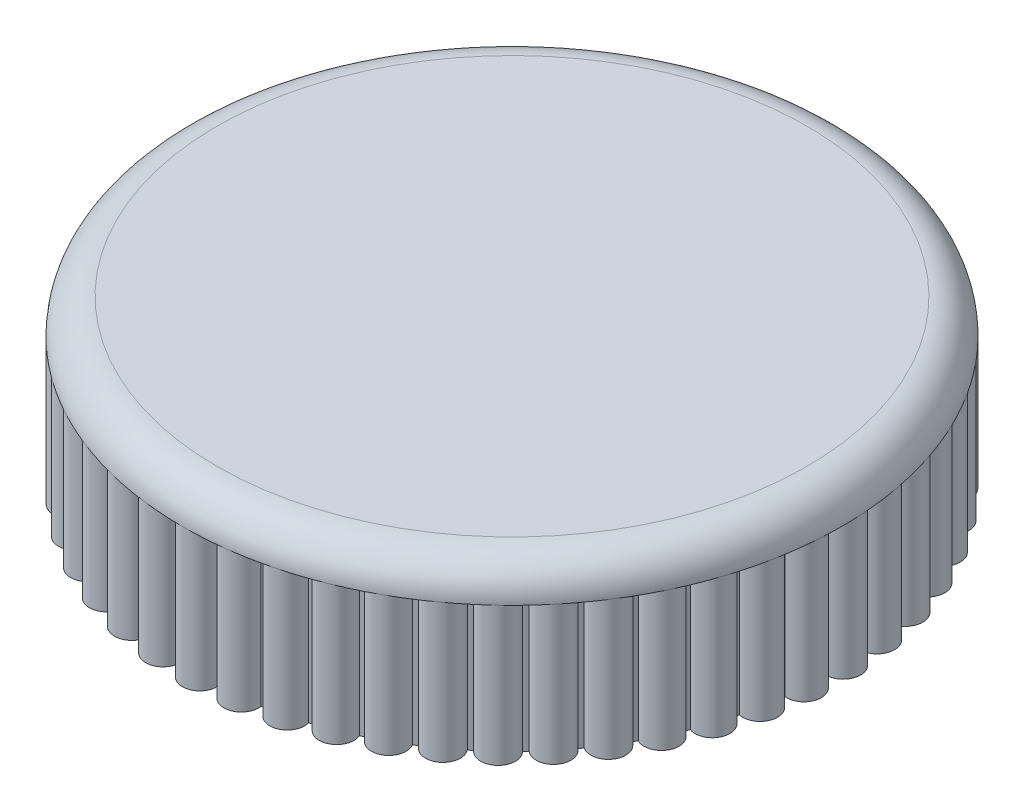
SolidWorks part; units mm, degrees
ref_plane "Front Plane" through (0, 0, 0) normal (0, 0, 1) x (1, 0, 0)
ref_plane "Top Plane" through (0, 0, 0) normal (0, 1, 0) x (1, 0, 0)
ref_plane "Right Plane" through (0, 0, 0) normal (1, 0, 0) x (0, 0, -1)
sketch "Sketch1" plane through (0, 0, 0) normal (0, 1, 0) x (1, 0, 0)
  circle A0 centre (0, 0) radius 24.13
  dimension "D1" = 48.26
extrude "Boss-Extrude3" add sketch "Sketch1" along normal blind 12.7
fillet "Fillet2" radius 2.54 1 edges at (0, 12.7, 24.13)
sketch "Sketch4" plane through (0, 0, 0) normal (0, 1, 0) x (1, 0, 0)
  circle A0 centre (0, 0) radius 22.86
  dimension "D1" = 45.72
extrude "Cut-Extrude3" cut sketch "Sketch4" along normal blind 10.16 flip side to cut
sketch "Sketch5" plane through (0, 0, 0) normal (0, 1, 0) x (1, 0, 0)
  circle A0 centre (0, 0) radius 19.05
  dimension "D1" = 38.1
extrude "Cut-Extrude4" cut sketch "Sketch5" along normal blind 10.16
sketch "Sketch6" plane through (0, 0, 0) normal (0, -1, 0) x (1, 0, 0)
  circle A0 centre (0, 22.86) radius 1.27
  circle A1 centre (0, 0) radius 22.86 construction
  circle A2 centre (0, 0) radius 22.86 construction
  dimension "D1" = 2.54
extrude "Boss-Extrude7" add sketch "Sketch6" against normal blind 10.16
pattern_circular "CirPattern1" count 50 over 360 about axis through (0, 0, 0) along (0, 1, 0) of "Boss-Extrude7"
